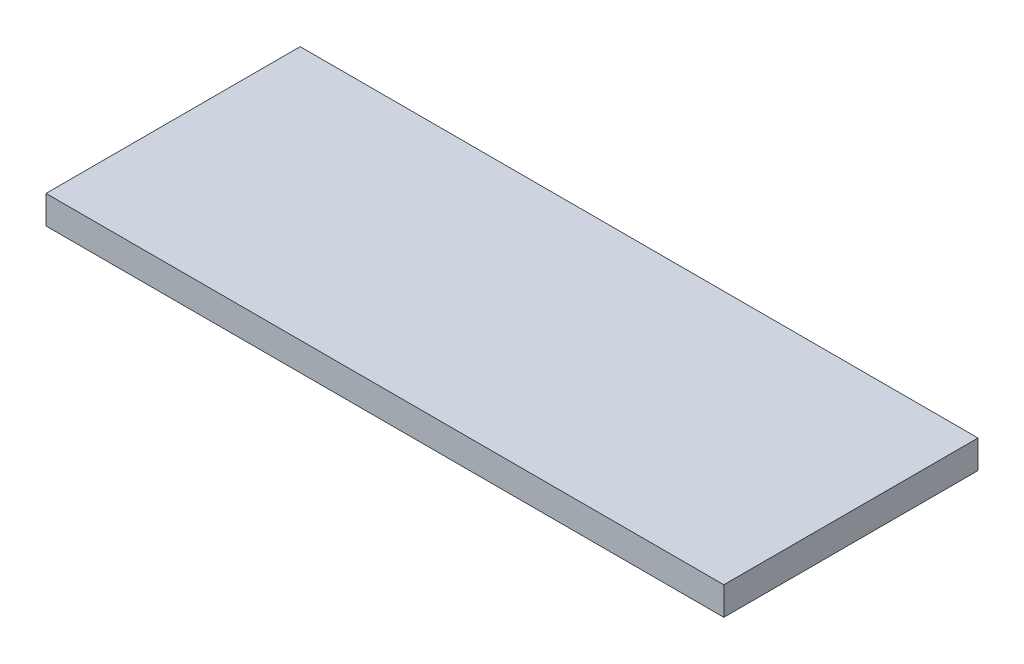
SolidWorks part; units mm, degrees
ref_plane "Front Plane" through (0, 0, 0) normal (0, 0, 1) x (1, 0, 0)
ref_plane "Top Plane" through (0, 0, 0) normal (0, 1, 0) x (1, 0, 0)
ref_plane "Right Plane" through (0, 0, 0) normal (1, 0, 0) x (0, 0, -1)
sketch "Sketch1" plane through (0, 0, 0) normal (0, 1, 0) x (1, 0, 0)
  line L1 (-52.2265, 96.9031) -> (252.5735, 96.9031)
  line L2 (-52.2265, 96.9031) -> (-52.2265, -17.3969)
  line L3 (-52.2265, -17.3969) -> (252.5735, -17.3969)
  line L4 (252.5735, 96.9031) -> (252.5735, -17.3969)
  dimension "D1" = 114.3
  dimension "D2" = 304.8
extrude "Boss-Extrude1" add sketch "Sketch1" along normal blind 12.7
